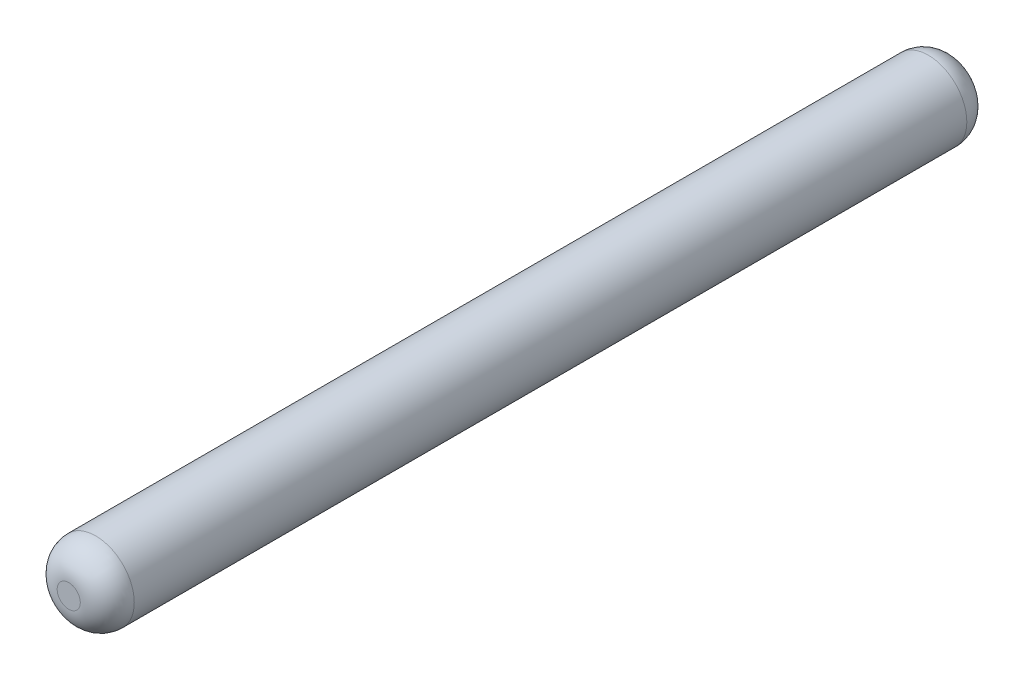
SolidWorks part; units mm, degrees
ref_plane "Plan de face" through (0, 0, 0) normal (0, 0, 1) x (1, 0, 0)
ref_plane "Plan de dessus" through (0, 0, 0) normal (0, 1, 0) x (1, 0, 0)
ref_plane "Plan de droite" through (0, 0, 0) normal (1, 0, 0) x (0, 0, -1)
sketch "Esquisse1" plane through (0, 0, 0) normal (0, 0, 1) x (1, 0, 0)
  circle A0 centre (0, 0) radius 1
extrude "Boss.-Extru.1" add sketch "Esquisse1" along normal blind 23
fillet "Congé1" radius 0.7 2 edges at (1, 0, 0) (1, 0, 23)
